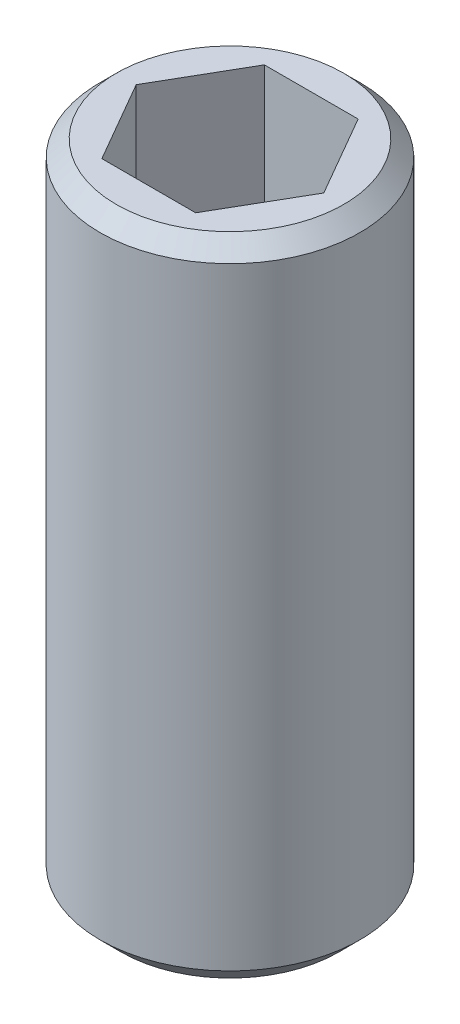
SolidWorks part; units mm, degrees
material "1023 Carbon Steel Sheet (SS)"
ref_plane "Front Plane" through (0, 0, 0) normal (0, 0, 1) x (1, 0, 0)
ref_plane "Top Plane" through (0, 0, 0) normal (0, 1, 0) x (1, 0, 0)
ref_plane "Right Plane" through (0, 0, 0) normal (1, 0, 0) x (0, 0, -1)
sketch "Sketch1" plane through (0, 0, 0) normal (0, 1, 0) x (1, 0, 0)
  circle A0 centre (0, 0) radius 4
  dimension "D1" = 8
extrude "Boss-Extrude1" add sketch "Sketch1" along normal blind 20
hole_wizard "Ø5.0mm Dowel Hole1" positions "Sketch3" profile "Sketch4" hole size "Ø5.0" standard "ISO"
sketch "Sketch3" plane through (0, 20, 0) normal (0, 1, 0) x (1, 0, 0)
  point P0 (0, 0)
sketch "Sketch4" plane through (0, 20, 0) normal (1, 0, 0) x (0, 0, 1)
  line L0 (0, 0) -> (0, 7.5022)
  line L1 (0, 7.5022) -> (2.5, 6)
  line L2 (2.5, 6) -> (2.5, 0)
  line L5 (2.5, 0) -> (0, 0)
  line L10 (0, 7.5022) -> (-2.5, 6) construction
  line L11 (0, -6.35) -> (0, 107.95) construction
  dimension "Hole Dia." = 5
  dimension "Hole Depth" = 6
  dimension "Drill Angle" = 118
sketch "Sketch2" plane through (0, 20, 0) normal (0, 1, 0) x (1, 0, 0)
  line L1 (2.8868, 0) -> (1.4434, 2.5)
  line L2 (1.4434, 2.5) -> (-1.4434, 2.5)
  line L3 (-1.4434, 2.5) -> (-2.8868, 0)
  line L4 (-2.8868, 0) -> (-1.4434, -2.5)
  line L5 (-1.4434, -2.5) -> (1.4434, -2.5)
  line L6 (1.4434, -2.5) -> (2.8868, 0)
  circle A0 centre (0, 0) radius 2.5 construction
  dimension "D1" = 5
extrude "Cut-Extrude1" cut sketch "Sketch2" against normal blind 6 contours L3 L4 L5 L6 L1 L2
chamfer "Chamfer1" distance 0.5 angle 45 1 edges at (0, 20, 4)
chamfer "Chamfer2" distance 0.65 angle 45 1 edges at (0, 0, 4)
